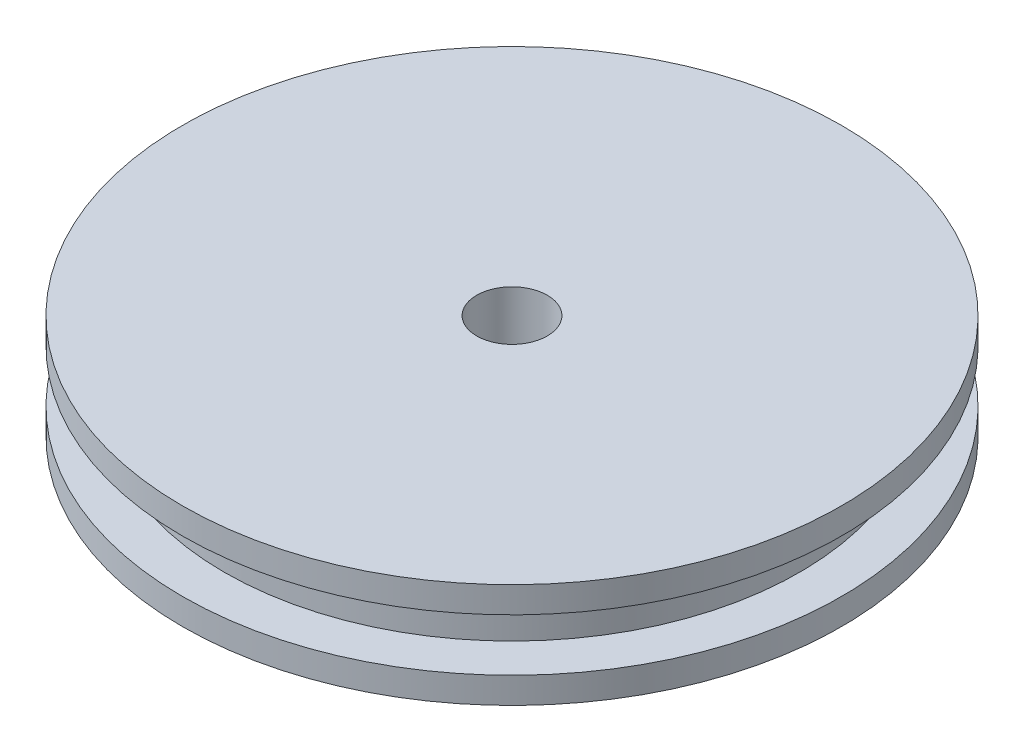
SolidWorks part; units mm, degrees
ref_plane "Plano frontal" through (0, 0, 0) normal (0, 0, 1) x (1, 0, 0)
ref_plane "Plano superior" through (0, 0, 0) normal (0, 1, 0) x (1, 0, 0)
ref_plane "Plano direito" through (0, 0, 0) normal (1, 0, 0) x (0, 0, -1)
sketch "Esboço1" plane through (0, 0, 0) normal (0, 1, 0) x (1, 0, 0)
  circle A0 centre (0, 0) radius 6.3
  dimension "D1" = 12.6
extrude "Ressalto-extrusão1" add sketch "Esboço1" along normal blind 0.5
sketch "Esboço10" plane through (0, 0.5, 0) normal (0, 1, 0) x (1, 0, 0)
  circle A0 centre (0, 0) radius 5.5
  dimension "D1" = 11
extrude "Ressalto-extrusão4" add sketch "Esboço10" along normal blind 1
sketch "Esboço11" plane through (0, 1.5, 0) normal (0, 1, 0) x (1, 0, 0)
  circle A0 centre (0, 0) radius 6.3
  dimension "D1" = 12.6
extrude "Ressalto-extrusão5" add sketch "Esboço11" along normal blind 0.5
sketch "Esboço12" plane through (0, 0, 0) normal (0, -1, 0) x (1, 0, 0)
  circle A0 centre (0, 0) radius 0.675
  dimension "D1" = 1.35
extrude "Corte-extrusão1" cut sketch "Esboço12" against normal up to next
